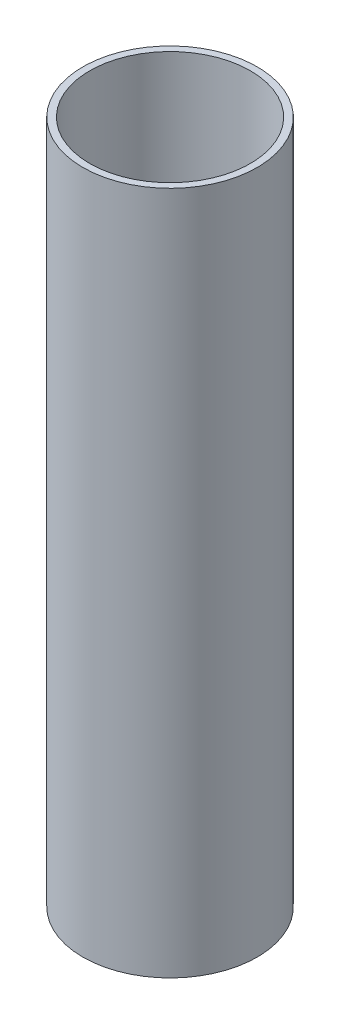
SolidWorks part; units mm, degrees
ref_plane "Front Plane" through (0, 0, 0) normal (0, 0, 1) x (1, 0, 0)
ref_plane "Top Plane" through (0, 0, 0) normal (0, 1, 0) x (1, 0, 0)
ref_plane "Right Plane" through (0, 0, 0) normal (1, 0, 0) x (0, 0, -1)
sketch "Sketch1" plane through (0, 0, 0) normal (0, 1, 0) x (1, 0, 0)
  circle A0 centre (0, 0) radius 25.5
  circle A1 centre (0, 0) radius 23.5
  dimension "D1" = 2
  dimension "D2" = 51
extrude "Boss-Extrude1" add sketch "Sketch1" along normal blind 200
sketch "Sketch2" plane through (0, 0, 0) normal (0, 0, 1) x (1, 0, 0)
  line L0 (-23.5, 0) -> (-5, 0)
  line L1 (-23.5, 0) -> (23.5, 0) construction
  line L2 (-25.5, 0) -> (25.5, 0) construction
  line L3 (0, 5) -> (0, 7)
  line L4 (-6.7082, 2) -> (-23.5, 2)
  line L5 (-23.5, 2) -> (-23.5, 0)
  arc A0 (-5, 0) -> (0, 5) centre (0, 0) cw
  arc A1 (0, 7) -> (-6.7082, 2) centre (0, 0) ccw
  dimension "D1" = 23.5
  dimension "D2" = 2
  dimension "D3" = 5
revolve "Revolve1" add sketch "Sketch2" angle 360 about L3
